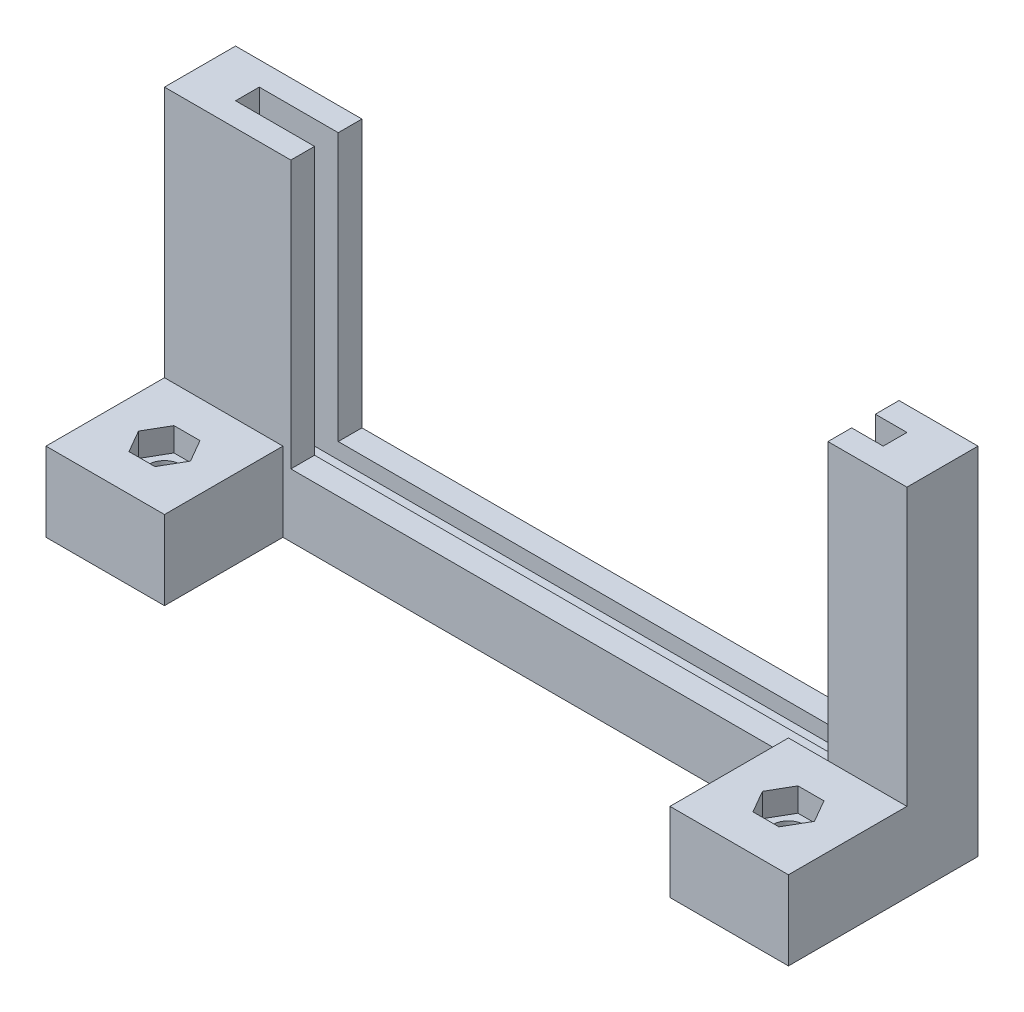
SolidWorks part; units mm, degrees
ref_plane "Plan de face" through (0, 0, 0) normal (0, 0, 1) x (1, 0, 0)
ref_plane "Plan de dessus" through (0, 0, 0) normal (0, 1, 0) x (1, 0, 0)
ref_plane "Plan de droite" through (0, 0, 0) normal (1, 0, 0) x (0, 0, -1)
sketch "Esquisse1" plane through (0, 0, 0) normal (0, 0, 1) x (1, 0, 0)
  line L17 (26.3064, -26.8419) -> (-41.6936, -26.8419)
  line L18 (26.3064, -26.8419) -> (26.3064, -34.8419) construction
  line L19 (26.3064, -34.8419) -> (-41.6936, -34.8419)
  line L20 (-41.6936, -26.8419) -> (-41.6936, -34.8419) construction
  line L21 (26.3064, 10.1581) -> (36.3064, 10.1581)
  line L22 (26.3064, 10.1581) -> (26.3064, -34.8419) construction
  line L23 (26.3064, -34.8419) -> (36.3064, -34.8419)
  line L24 (36.3064, 10.1581) -> (36.3064, -34.8419)
  line L26 (-41.6936, 7.0239) -> (-41.6936, -26.8419)
  line L27 (-41.6936, -34.8419) -> (-57.6936, -34.8419)
  line L28 (-41.6936, -34.8419) -> (-41.6936, 7.0239) construction
  line L29 (-41.6936, 7.0239) -> (-57.6936, 7.0239)
  line L30 (-57.6936, -34.8419) -> (-57.6936, 7.0239)
  line L31 (26.3064, 10.1581) -> (26.3064, -26.8419)
  dimension "D1" = 45
  dimension "D2" = 78
  dimension "D3" = 10
  dimension "D4" = 8
  dimension "D5" = 16
extrude "Boss.-Extru.1" add sketch "Esquisse1" along normal blind 3
sketch "Esquisse2" plane through (0, 0, 3) normal (0, 0, 1) x (1, 0, 0)
  line L0 (-57.6936, 7.0239) -> (-57.6936, -34.8419)
  line L1 (-57.6936, -34.8419) -> (36.3064, -34.8419)
  line L2 (36.3064, -34.8419) -> (36.3064, 10.1581)
  line L3 (36.3064, 10.1581) -> (30.3064, 10.1581)
  line L4 (36.3064, 10.1581) -> (26.3064, 10.1581) construction
  line L5 (30.3064, 10.1581) -> (30.3064, -28.8419)
  line L6 (30.3064, -28.8419) -> (-51.6936, -28.8419)
  line L7 (-51.6936, -28.8419) -> (-51.6936, 7.0239)
  line L8 (-41.6936, 7.0239) -> (-57.6936, 7.0239) construction
  line L9 (-51.6936, 7.0239) -> (-57.6936, 7.0239)
  dimension "D1" = 6
  dimension "D2" = 6
  dimension "D3" = 6
extrude "Boss.-Extru.2" add sketch "Esquisse2" along normal blind 1.5
ref_plane "Plan1" through (0, 0, 4.5) normal (0, 0, 1) x (1, 0, 0)
mirror "Symétrie3" about plane through (0, 0, 4.5) normal (0, 0, 1) of bodies 105
sketch "Esquisse3" plane through (0, -34.8419, 0) normal (0, -1, 0) x (1, 0, 0)
  line L1 (-57.6936, 9) -> (-42.6936, 9)
  line L2 (-57.6936, 9) -> (-57.6936, 24)
  line L3 (-57.6936, 24) -> (-42.6936, 24)
  line L4 (-42.6936, 9) -> (-42.6936, 24)
  line L5 (36.3064, 9) -> (21.3064, 9)
  line L6 (36.3064, 9) -> (36.3064, 24)
  line L7 (36.3064, 24) -> (21.3064, 24)
  line L8 (21.3064, 9) -> (21.3064, 24)
  dimension "D1" = 15
  dimension "D2" = 15
  dimension "D3" = 15
  dimension "D4" = 15
extrude "Boss.-Extru.3" add sketch "Esquisse3" against normal blind 10
sketch "Esquisse4" plane through (0, -24.8419, 0) normal (0, 1, 0) x (1, 0, 0)
  line L0 (-57.6936, -9) -> (-42.6936, -24) construction
  line L1 (36.3064, -9) -> (21.3064, -24) construction
  circle A0 centre (-50.1936, -16.5) radius 2
  circle A1 centre (28.8064, -16.5) radius 2
  dimension "D1" = 4
extrude "Enlèv. mat.-Extru.1" cut sketch "Esquisse4" against normal blind 10
sketch "Esquisse5" plane through (0, -24.8419, 0) normal (0, 1, 0) x (1, 0, 0)
  line L0 (-51.839, -13.65) -> (-48.5481, -13.65)
  line L1 (-48.5481, -13.65) -> (-46.9027, -16.5)
  line L3 (-48.5481, -19.35) -> (-51.839, -19.35)
  line L4 (-51.839, -19.35) -> (-53.4845, -16.5)
  line L5 (-53.4845, -16.5) -> (-51.839, -13.65)
  line L6 (-46.9027, -16.5) -> (-48.5481, -19.35)
  line L7 (-53.4845, -16.5) -> (-46.9027, -16.5) construction
  line L8 (27.161, -13.65) -> (30.4519, -13.65)
  line L9 (30.4519, -13.65) -> (32.0973, -16.5)
  line L10 (30.4519, -19.35) -> (27.161, -19.35)
  line L11 (27.161, -19.35) -> (25.5155, -16.5)
  line L12 (25.5155, -16.5) -> (27.161, -13.65)
  line L13 (32.0973, -16.5) -> (30.4519, -19.35)
  line L14 (25.5155, -16.5) -> (32.0973, -16.5) construction
  point P2 (-50.1936, -16.5)
  point P7 (-50.1936, -16.5)
  point P8 (28.8064, -16.5)
  point P11 (28.8064, -16.5)
  dimension "D1" = 5.7
  dimension "D2" = 120
  dimension "D3" = 5.7
  dimension "D4" = 120
extrude "Enlèv. mat.-Extru.2" cut sketch "Esquisse5" against normal blind 3
